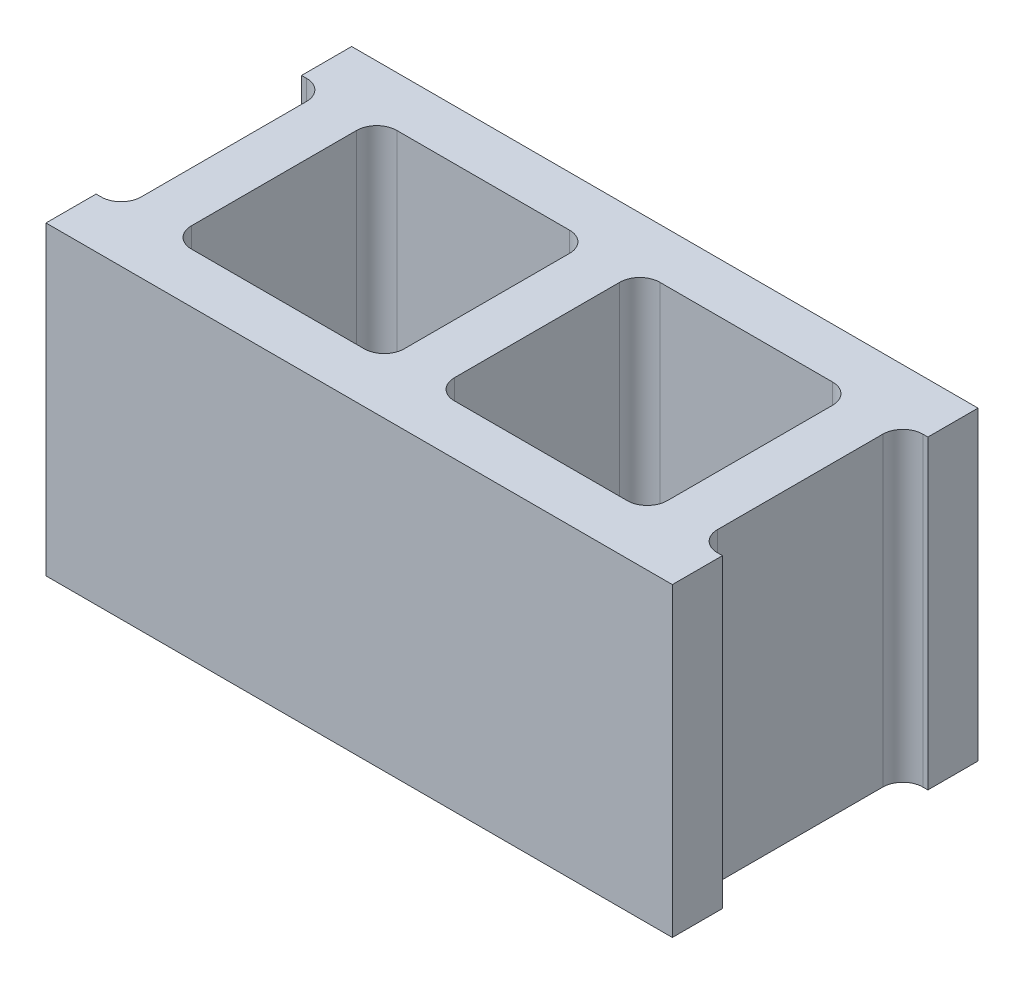
SolidWorks part; units mm, degrees
ref_plane "Front Plane" through (0, 0, 0) normal (0, 0, 1) x (1, 0, 0)
ref_plane "Top Plane" through (0, 0, 0) normal (0, 1, 0) x (1, 0, 0)
ref_plane "Right Plane" through (0, 0, 0) normal (1, 0, 0) x (0, 0, -1)
sketch "Sketch1" plane through (0, 0, 0) normal (0, 1, 0) x (1, 0, 0)
  line L0 (-198.4375, 65.0875) -> (-195.2625, 65.0875)
  line L1 (198.4375, -96.8375) -> (-198.4375, -96.8375)
  line L2 (198.4375, -96.8375) -> (198.4375, -65.0875)
  line L3 (198.4375, 96.8375) -> (-198.4375, 96.8375)
  line L4 (-198.4375, -96.8375) -> (-198.4375, -65.0875)
  line L5 (198.4375, -96.8375) -> (-198.4375, 96.8375) construction
  line L6 (198.4375, 96.8375) -> (-198.4375, -96.8375) construction
  line L7 (-182.5625, 52.3875) -> (-182.5625, -52.3875)
  line L8 (-195.2625, -65.0875) -> (-198.4375, -65.0875)
  line L9 (-198.4375, 65.0875) -> (-198.4375, 96.8375)
  line L10 (198.4375, 65.0875) -> (195.2625, 65.0875)
  line L11 (182.5625, 52.3875) -> (182.5625, -52.3875)
  line L12 (195.2625, -65.0875) -> (198.4375, -65.0875)
  line L13 (198.4375, 65.0875) -> (198.4375, 96.8375)
  line L14 (-182.5625, 0) -> (182.5625, 0) construction
  line L16 (-28.575, -65.0875) -> (-138.1125, -65.0875)
  line L17 (-15.875, -52.3875) -> (-15.875, 52.3875)
  line L18 (-28.575, 65.0875) -> (-138.1125, 65.0875)
  line L19 (-150.8125, -52.3875) -> (-150.8125, 52.3875)
  line L20 (-15.875, -65.0875) -> (-150.8125, 65.0875) construction
  line L21 (-15.875, 65.0875) -> (-150.8125, -65.0875) construction
  line L22 (138.1125, -65.0875) -> (28.575, -65.0875)
  line L23 (150.8125, -52.3875) -> (150.8125, 52.3875)
  line L24 (138.1125, 65.0875) -> (28.575, 65.0875)
  line L25 (15.875, -52.3875) -> (15.875, 52.3875)
  line L26 (150.8125, -65.0875) -> (15.875, 65.0875) construction
  line L27 (150.8125, 65.0875) -> (15.875, -65.0875) construction
  arc A0 (-182.5625, 52.3875) -> (-195.2625, 65.0875) centre (-195.2625, 52.3875) ccw
  arc A1 (-195.2625, -65.0875) -> (-182.5625, -52.3875) centre (-195.2625, -52.3875) ccw
  arc A2 (-138.1125, -65.0875) -> (-150.8125, -52.3875) centre (-138.1125, -52.3875) cw
  arc A3 (-138.1125, 65.0875) -> (-150.8125, 52.3875) centre (-138.1125, 52.3875) ccw
  arc A4 (-15.875, 52.3875) -> (-28.575, 65.0875) centre (-28.575, 52.3875) ccw
  arc A5 (-28.575, -65.0875) -> (-15.875, -52.3875) centre (-28.575, -52.3875) ccw
  arc A6 (28.575, 65.0875) -> (15.875, 52.3875) centre (28.575, 52.3875) ccw
  arc A7 (150.8125, 52.3875) -> (138.1125, 65.0875) centre (138.1125, 52.3875) ccw
  arc A8 (138.1125, -65.0875) -> (150.8125, -52.3875) centre (138.1125, -52.3875) ccw
  arc A9 (15.875, -52.3875) -> (28.575, -65.0875) centre (28.575, -52.3875) ccw
  arc A10 (182.5625, 52.3875) -> (195.2625, 65.0875) centre (195.2625, 52.3875) cw
  arc A11 (195.2625, -65.0875) -> (182.5625, -52.3875) centre (195.2625, -52.3875) cw
  point P0 (0, 0)
  point P16 (-83.3438, 0)
  point P21 (83.3438, 0)
  point P28 (-182.5625, 65.0875)
  point P31 (-182.5625, -65.0875)
  dimension "D8" = 12.7
  dimension "D10" = 12.7
  dimension "D1" = 193.675
  dimension "D2" = 396.875
  dimension "D3" = 31.75
  dimension "D4" = 15.875
  dimension "D5" = 31.75
  dimension "D6" = 31.75
  dimension "D7" = 15.875
  dimension "D9" = 15.875
extrude "Extrude1" add sketch "Sketch1" along normal blind 193.675
